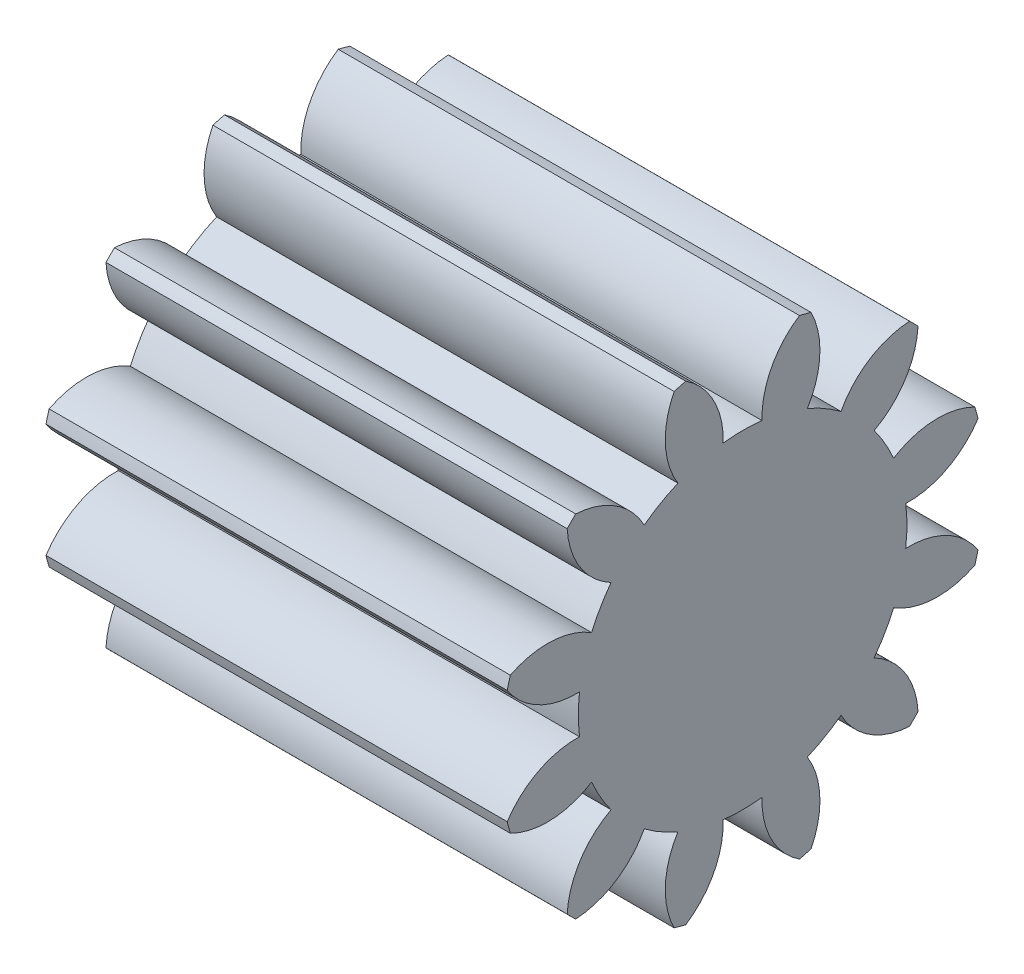
SolidWorks part; units mm, degrees
ref_plane "Plane1" through (0, 0, 0) normal (0, 0, 1) x (1, 0, 0)
ref_plane "Plane2" through (0, 0, 0) normal (0, 1, 0) x (1, 0, 0)
ref_plane "Plane3" through (0, 0, 0) normal (1, 0, 0) x (0, 0, -1)
other "Configuration Table"
sketch "HoldingSke" plane through (0, 0, 0) normal (0, 1, 0) x (1, 0, 0)
  line L0 (0, 0) -> (1.0868, -0.231)
  line L1 (-15, 0) -> (100, 0) construction
  line L2 (0, 0) -> (-2.1039, 2.3779)
  line L3 (0, 0) -> (-11.863, 4.5341)
  line L4 (0, 0) -> (8.4473, 1.7955)
  line L5 (0, 0) -> (-46.8476, -17.4728)
  line L6 (0, 0) -> (-9.9476, -6.7116)
  line L7 (-2.1039, 2.3779) -> (8.6586, 51.2059)
  line L8 (-76.2, 54.61) -> (-75.3, 54.61)
  line L9 (-71.009, 38.7566) -> (-53.1078, 45.2721)
  line L10 (-76.2, 71.12) -> (104.1128, 71.12)
  line L11 (0, 0) -> (-12, 0)
  line L12 (-76.2, 101.6) -> (-76.166, 101.6)
  line L13 (24.9733, 27.94) -> (52.9518, 28.4284)
  line L14 (24.9733, 27.94) -> (24.9743, 27.94)
  line L15 (24.9733, 27.94) -> (100.4006, 29.5858)
  line L16 (-63.627, -0.9) -> (-12.827, -0.9)
  circle A0 centre (0, 0) radius 2.5
  circle A1 centre (0, 0) radius 4.274
  circle A2 centre (0, 0) radius 37.5
  circle A3 centre (0, 0) radius 2.5
  dimension "MHD" = 8.548
  dimension "Hub_dia" = 75
  dimension "Bore" = 5
  dimension "MBD" = 5
  dimension "Num_teeth" = 12
  dimension "Pitch" = 1.1111
  dimension "Overall_len" = 50
  dimension "Show_teeth" = 12
  dimension "Thickness" = 12
  dimension "OAL" = 50.0001
  dimension "T_dim" = 0.9
  dimension "Ap" = 20
  dimension "H" = 19.05
  dimension "Pitch_radius" = 180.3128
  dimension "Width" = 12
  dimension "Backlash" = 0.034
  dimension "Addendum_fac" = 1
  dimension "Dedendum_fac" = 1.25
  dimension "Clearance_fac" = 0.25
  dimension "Dedendum_add" = 0.001
  dimension "Module" = 0.9
sketch "BasProSke" plane through (0, 0, 0) normal (0, 1, 0) x (1, 0, 0)
  line L0 (-10, 0) -> (60, 0) construction
  line L1 (0, 0) -> (0, 6.3)
  line L2 (0, 0) -> (12, 0)
  line L3 (12, 0) -> (12, 6.3)
  line L4 (12, 6.3) -> (0, 6.3)
  dimension "Thickness" = 12
  dimension "Diameter" = 12.6
revolve "Base-Revolve" add sketch "BasProSke" angle 360 about L0
sketch "TooCutSke" plane through (0, 0, 0) normal (1, 0, 0) x (0, 0, -1)
  line L1 (0, 0) -> (0, 107) construction
  line L2 (0, 0) -> (-0.7643, 5.3456) construction
  line L3 (0, 0) -> (-2.7752, 10.3572) construction
  line L4 (-0.7643, 5.3456) -> (-1.3876, 5.1786) construction
  arc A0 (0.5057, 4.244) -> (-0.5057, 4.244) centre (0, 0) ccw
  arc A1 (1.5081, 6.143) -> (-1.5081, 6.143) centre (0, 0) ccw
  circle A2 centre (0, 0) radius 5.4 construction
  circle A3 centre (0, 0) radius 5.0743 construction
  arc A4 (-0.5057, 4.244) -> (-1.5081, 6.143) centre (-2.6644, 4.3185) ccw
  arc A5 (1.5081, 6.143) -> (0.5057, 4.244) centre (2.6644, 4.3185) ccw
  dimension "Root_dia" = 8.548
  dimension "Overcut_dia" = 12.6508
  dimension "Pitch_dia" = 10.8
  dimension "Base_dia" = 10.1487
  dimension "Flank_rad" = 2.16
  dimension "Half_ang" = 15
  dimension "Half_CT" = 0.6453
extrude "ToothCut" cut sketch "TooCutSke" along normal through all
fillet "Breaks" [suppressed] radius 0.018
fillet "RootFillets" [suppressed] radius 0.226
pattern_circular "TeethCuts" count 12 every 30 about axis through (-10, 0, 0) along (1, 0, 0) of "ToothCut", "RootFillets", "Breaks"
sketch "HubNeaOneSke" plane through (0, 0, 0) normal (-1, 0, 0) x (0, 0, 1)
  circle A0 centre (0, 0) radius 4.274
  dimension "Diameter" = 8.548
extrude "HubNearOne" [suppressed] add sketch "HubNeaOneSke" along normal blind 38.0001
sketch "HubNeaBotSke" plane through (0, 0, 0) normal (-1, 0, 0) x (0, 0, 1)
  circle A0 centre (0, 0) radius 4.274
  dimension "Diameter" = 8.548
extrude "HubNearBoth" [suppressed] add sketch "HubNeaBotSke" along normal blind 19
ref_plane "FarPln" through (12, 0, 0) normal (1, 0, 0) x (0, 0, -1)
sketch "HubFarSke" plane through (12, 0, 0) normal (1, 0, 0) x (0, 0, -1)
  circle A0 centre (0, 0) radius 4.274
  dimension "Diameter" = 8.548
extrude "HubFar" [suppressed] add sketch "HubFarSke" along normal blind 19
sketch "BorSke" plane through (0, 0, 0) normal (1, 0, 0) x (0, 0, -1)
  line L0 (-1.5, 2) -> (1.5, 2)
  line L1 (0, 2) -> (0, -2.5) construction
  arc A0 (-1.5, 2) -> (1.5, 2) centre (0, 0) ccw
  dimension "Diameter" = 5
  dimension "D1" = 4.5
extrude "Bore" cut sketch "BorSke" along normal mid plane 100.0001
sketch "KeySke" plane through (0, 0, 0) normal (1, 0, 0) x (0, 0, -1)
  line L0 (-1, 0) -> (-1, 3.4)
  line L1 (-1, 3.4) -> (1, 3.4)
  line L2 (1, 3.4) -> (1, 0)
  line L3 (0, 0) -> (0, 34) construction
  line L4 (-1, 0) -> (1, 0)
  dimension "Offset" = 3.4
  dimension "Width" = 2
extrude "Keyway" [suppressed] cut sketch "KeySke" along normal mid plane 100.0001
pattern_circular "Keyway2" [suppressed] count 2 every 90 about axis through (-10, 0, 0) along (1, 0, 0)
sketch "Sketch1" plane through (12, 0, 0) normal (1, 0, 0) x (0, 0, -1)
  line L0 (1.5, 2) -> (-1.5, 2) construction
  line L1 (1.5, 2) -> (-1.5, 2)
  arc A0 (-1.5, 2) -> (1.5, 2) centre (0, 0) ccw construction
  arc A1 (-1.5, 2) -> (1.5, 2) centre (0, 0) ccw
extrude "Boss-Extrude1" add sketch "Sketch1" against normal up to surface (12 mm away) up to face at (0, 0, 0)
equation "' \"Module@HoldingSke\" = 6.35"
equation "' \"Num_teeth@HoldingSke\" = 12"
equation "' \"Ap@HoldingSke\" =  20"
equation "' \"Ap@HoldingSke\" = 20"
equation "' \"Width@HoldingSke\" = 0.5 * 25.4"
equation "' \"Hub_dia@HoldingSke\"= 1 * 25.4"
equation "' \"Hub_dia@HoldingSke\" = 1 * 25.4"
equation "' \"Overall_len@HoldingSke\" = 1.0 * 25.4"
equation "' \"Bore@HoldingSke\" = 0.75 * 25.4"
equation "' \"T_dim@HoldingSke\" = 0.1 * 25.4"
equation "' \"Width@KeySke\" = 0.25 * 25.4"
equation "' \"Show_teeth@HoldingSke\" = 13"
equation "' \"Backlash@HoldingSke\" = 0.009 * 25.4"
equation "' \"Addendum_fac@HoldingSke\" = 1.0"
equation "' \"Dedendum_fac@HoldingSke\" = 1.25"
equation "' \"Dedendum_add@HoldingSke\" = 0.00005 * 25.4"
equation "' \"Clearance_fac@HoldingSke\" = 0.25"
equation "\"Pitch@HoldingSke\" = 1 / \"Module@HoldingSke\""
equation "\"Overcut_dia@TooCutSke\" = (\"Num_teeth@HoldingSke\" + 2 * \"Addendum_fac@HoldingSke\") / \"Pitch@HoldingSke\" + 0.002 * 25.4"
equation "\"Pitch_dia@TooCutSke\" = \"Num_teeth@HoldingSke\" / \"Pitch@HoldingSke\""
equation "\"Base_dia@TooCutSke\" = \"Num_teeth@HoldingSke\" / \"Pitch@HoldingSke\" * cos((\"Ap@HoldingSke\"  * 3.14159265 / 180))"
equation "\"Root_dia@TooCutSke\" = (\"Num_teeth@HoldingSke\" + 2) / \"Pitch@HoldingSke\" - 2 * (\"Addendum_fac@HoldingSke\" + \"Dedendum_fac@HoldingSke\") / \"Pitch@HoldingSke\" - \"Dedendum_add@HoldingSke\" * 2"
equation "\"Half_ang@TooCutSke\" = 180 / \"Num_teeth@HoldingSke\""
equation "\"Half_CT@TooCutSke\" = \"Num_teeth@HoldingSke\" / \"Pitch@HoldingSke\" * sin((3.14159265 / 2 / \"Num_teeth@HoldingSke\")) / 2 - 7 * \"Backlash@HoldingSke\" / 4"
equation "\"Flank_rad@TooCutSke\" = \"Num_teeth@HoldingSke\" / \"Pitch@HoldingSke\" / 5"
equation "\"Radius@RootFillets\" = \"Clearance_fac@HoldingSke\" / \"Pitch@HoldingSke\" + \"Dedendum_add@HoldingSke\""
equation "\"Break_rad@Breaks\" = 0.02 / \"Pitch@HoldingSke\""
equation "\"Thickness@HoldingSke\" = \"Width@HoldingSke\""
equation "\"OAL@HoldingSke\" = \"Thickness@HoldingSke\""
equation "\"MHD@HoldingSke\" = (\"Num_teeth@HoldingSke\" + 2) / \"Pitch@HoldingSke\" - 2 * (\"Addendum_fac@HoldingSke\" + \"Dedendum_fac@HoldingSke\")  / \"Pitch@HoldingSke\" - \"Dedendum_add@HoldingSke\" * 2"
equation "\"MBD@HoldingSke\" = (\"Num_teeth@HoldingSke\" + 2) / \"Pitch@HoldingSke\" - 2 * (\"Addendum_fac@HoldingSke\" + \"Dedendum_fac@HoldingSke\")  / \"Pitch@HoldingSke\" - \"Dedendum_add@HoldingSke\" * 2 - 0.002 * 25.4"
equation "\"MHD@HoldingSke\" = ((sgn( \"MHD@HoldingSke\" - \"Hub_dia@HoldingSke\" )-1)*( \"MHD@HoldingSke\" - \"Hub_dia@HoldingSke\" ))/-2+ \"Hub_dia@HoldingSke\""
equation "\"MBD@HoldingSke\" = ((sgn( \"MBD@HoldingSke\" - \"Bore@HoldingSke\" )-1)*( \"MBD@HoldingSke\" - \"Bore@HoldingSke\" ))/-2+ \"Bore@HoldingSke\""
equation "\"OAL@HoldingSke\" = ((sgn( \"OAL@HoldingSke\" - \"Overall_len@HoldingSke\" )+1)*( \"OAL@HoldingSke\" - \"Overall_len@HoldingSke\" ))/2 + \"Overall_len@HoldingSke\" + 0.000002 * 25.4"
equation "\"Num_teeth@TeethCuts\" = int( \"Show_teeth@HoldingSke\" ) + 1"
equation "\"Num_teeth@TeethCuts\" = ((sgn( \"Num_teeth@TeethCuts\" - \"Num_teeth@HoldingSke\" )-1)*( \"Num_teeth@TeethCuts\" - \"Num_teeth@HoldingSke\" ))/-2+ \"Num_teeth@HoldingSke\""
equation "\"Num_teeth@TeethCuts\" = ((sgn( \"Num_teeth@TeethCuts\" - 2.0)+1)*( \"Num_teeth@TeethCuts\" - 2.0))/2 +2.0"
equation "\"Angle@TeethCuts\" = 360.0 / \"Num_teeth@HoldingSke\""
equation "\"Diameter@BasProSke\" = (\"Num_teeth@HoldingSke\" + 2 * \"Addendum_fac@HoldingSke\") / \"Pitch@HoldingSke\""
equation "\"Thickness@BasProSke\"  = \"Thickness@HoldingSke\""
equation "' \"Fillet_rad@BasProSke\" =  \"Thickness@HoldingSke\" * 0.05"
equation "' \"Fillet_rad@BasProSke\" = \"Thickness@HoldingSke\" * 0.05"
equation "\"MHD@HoldingSke\" = ((sgn( \"MHD@HoldingSke\" - \"Root_dia@TooCutSke\" )-1)*( \"MHD@HoldingSke\" - \"Root_dia@TooCutSke\" ))/-2+ \"Root_dia@TooCutSke\""
equation "\"Diameter@HubNeaOneSke\" = \"MHD@HoldingSke\""
equation "\"Length@HubNearOne\" = \"OAL@HoldingSke\" - \"Thickness@BasProSke\""
equation "\"Diameter@HubNeaBotSke\" = \"MHD@HoldingSke\""
equation "\"Length@HubNearBoth\" = ( \"OAL@HoldingSke\" - \"Thickness@BasProSke\" ) / 2.0"
equation "\"Thickness@FarPln\" = \"Thickness@BasProSke\""
equation "\"Diameter@HubFarSke\" = \"MHD@HoldingSke\""
equation "\"Length@HubFar\" = ( \"OAL@HoldingSke\" - \"Thickness@BasProSke\" ) / 2.0"
equation "\"Diameter@BorSke\" = \"MBD@HoldingSke\""
equation "\"D1@Bore\" = \"OAL@HoldingSke\" * 2.0"
equation "\"D1@Keyway\" = \"OAL@HoldingSke\" * 2.0"
equation "\"Offset@KeySke\" = \"T_dim@HoldingSke\" + \"MBD@HoldingSke\" / 2.0"
